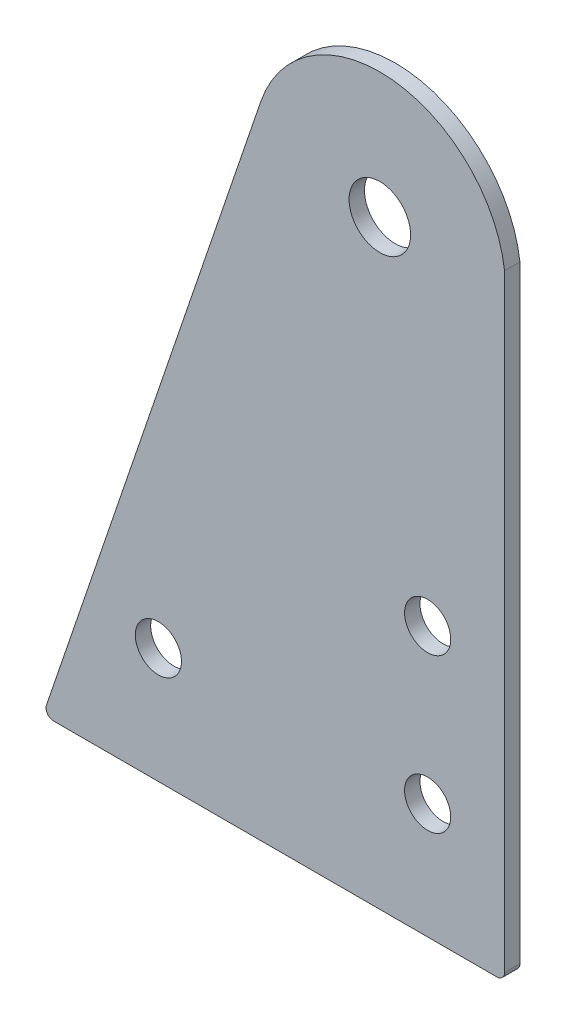
SolidWorks part; units mm, degrees
ref_plane "前视基准面" through (0, 0, 0) normal (0, 0, 1) x (1, 0, 0)
ref_plane "上视基准面" through (0, 0, 0) normal (0, 1, 0) x (1, 0, 0)
ref_plane "右视基准面" through (0, 0, 0) normal (1, 0, 0) x (0, 0, -1)
sketch "草图1" plane through (0, 0, 0) normal (0, 0, 1) x (1, 0, 0)
  line L0 (0, 0) -> (0, 80)
  line L1 (-60, 0) -> (-31.69, 83.1971)
  line L2 (-60, 0) -> (0, 0)
  arc A0 (0, 75.8626) -> (-31.69, 83.1971) centre (-16.215, 77.9313) ccw
  dimension "D1" = 80
  dimension "D2" = 60
extrude "凸台-拉伸1" add sketch "草图1" along normal blind 2 contours L0 A0 L1 L2
fillet "圆角1" radius 1 2 edges at (0, 0, 1) (-60, 0, 1)
sketch "草图2" plane through (0, 0, 2) normal (0, 0, 1) x (1, 0, 0)
  line L0 (0, 1) -> (0, 80) construction
  line L1 (-58.6034, 0) -> (-1, 0) construction
  circle A0 centre (-16.215, 77.9313) radius 4
  arc A1 (0, 80) -> (-31.69, 83.1971) centre (-16.215, 77.9313) ccw construction
  circle A2 centre (-10, 35) radius 3
  circle A3 centre (-10, 15) radius 3
  circle A4 centre (-45, 15) radius 3
  dimension "D1" = 8
  dimension "D2" = 6
  dimension "D3" = 10
  dimension "D4" = 20
  dimension "D5" = 35
  dimension "D6" = 15
extrude "切除-拉伸1" cut sketch "草图2" against normal blind 2
